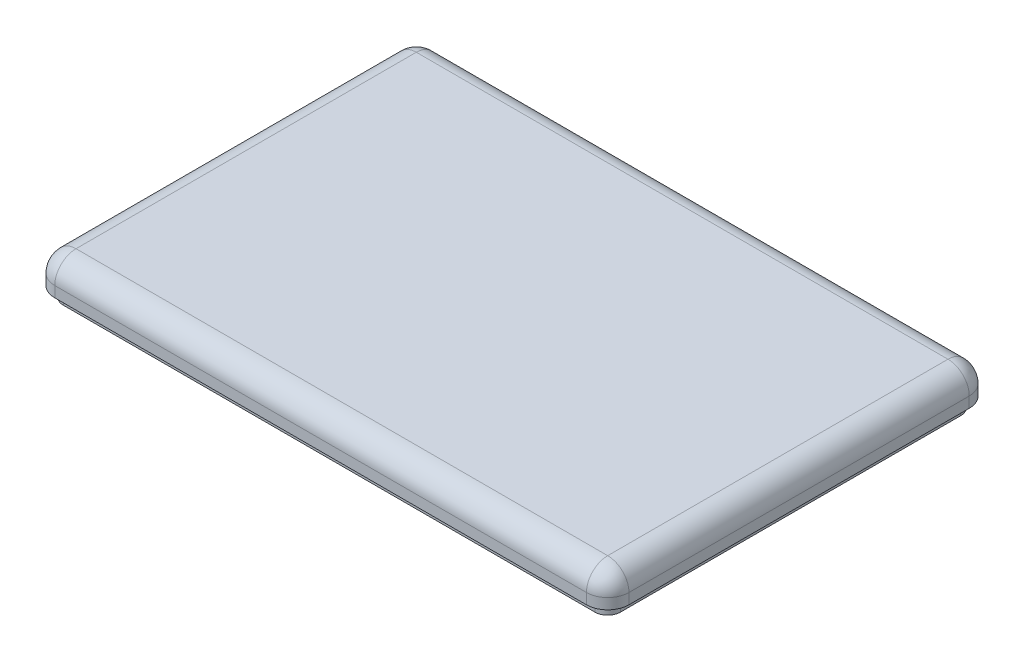
SolidWorks part; units mm, degrees
ref_plane "前视基准面" through (0, 0, 0) normal (0, 0, 1) x (1, 0, 0)
ref_plane "上视基准面" through (0, 0, 0) normal (0, 1, 0) x (1, 0, 0)
ref_plane "右视基准面" through (0, 0, 0) normal (1, 0, 0) x (0, 0, -1)
sketch "Sketch1" plane through (0, 0, 0) normal (0, 1, 0) x (1, 0, 0)
  line L1 (-135, -90) -> (135, -90)
  line L2 (-135, -90) -> (-135, 90)
  line L3 (-135, 90) -> (135, 90)
  line L4 (135, -90) -> (135, 90)
  line L5 (-135, -90) -> (135, 90) construction
  line L6 (-135, 90) -> (135, -90) construction
  point P0 (0, 0)
  dimension "D1" = 270
  dimension "D2" = 180
extrude "Extrude1" add sketch "Sketch1" along normal blind 20
fillet "Fillet1" radius 10 8 edges at (-135, 10, 90) (-135, 10, -90) (135, 10, -90) (135, 10, 90) (135, 20, 0) (0, 20, -90) (-135, 20, 0) (0, 20, 90)
sketch "Sketch3" plane through (0, 0, 0) normal (0, -1, 0) x (1, 0, 0)
  line L0 (-131, 80) -> (-131, -80)
  line L1 (-125, -86) -> (125, -86)
  line L2 (131, -80) -> (131, 80)
  line L3 (125, 86) -> (-125, 86)
  line L4 (125, 90) -> (-125, 90)
  line L5 (-135, 80) -> (-135, -80)
  line L6 (-125, -90) -> (125, -90)
  line L7 (135, -80) -> (135, 80)
  line L8 (125, 90) -> (-125, 90)
  line L9 (-135, 80) -> (-135, -80)
  line L10 (-125, -90) -> (125, -90)
  line L11 (135, -80) -> (135, 80)
  arc A0 (-131, -80) -> (-125, -86) centre (-125, -80) ccw
  arc A1 (125, -86) -> (131, -80) centre (125, -80) ccw
  arc A2 (131, 80) -> (125, 86) centre (125, 80) ccw
  arc A3 (-125, 86) -> (-131, 80) centre (-125, 80) ccw
  arc A4 (-125, 90) -> (-135, 80) centre (-125, 80) ccw
  arc A5 (-135, -80) -> (-125, -90) centre (-125, -80) ccw
  arc A6 (125, -90) -> (135, -80) centre (125, -80) ccw
  arc A7 (135, 80) -> (125, 90) centre (125, 80) ccw
  arc A8 (-125, 90) -> (-135, 80) centre (-125, 80) ccw
  arc A9 (-135, -80) -> (-125, -90) centre (-125, -80) ccw
  arc A10 (125, -90) -> (135, -80) centre (125, -80) ccw
  arc A11 (135, 80) -> (125, 90) centre (125, 80) ccw
  dimension "D1" = 0
  dimension "D2" = 4
extrude "Extrude3" cut sketch "Sketch3" against normal blind 5
